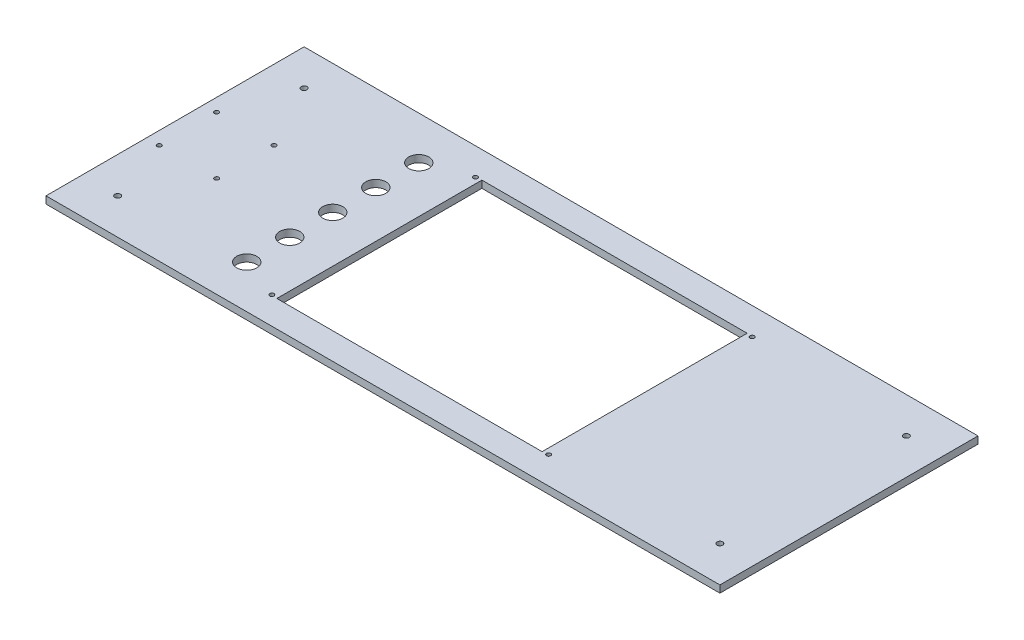
SolidWorks part; units mm, degrees
ref_plane "前视基准面" through (0, 0, 0) normal (0, 0, 1) x (1, 0, 0)
ref_plane "上视基准面" through (0, 0, 0) normal (0, 1, 0) x (1, 0, 0)
ref_plane "右视基准面" through (0, 0, 0) normal (1, 0, 0) x (0, 0, -1)
sketch "草图1" plane through (0, 0, 0) normal (0, 1, 0) x (1, 0, 0)
  line L0 (0, 105) -> (0, -75) construction
  line L1 (-235, 105) -> (235, 105)
  line L2 (-235, 105) -> (-235, -75)
  line L3 (-235, -75) -> (235, -75)
  line L4 (235, 105) -> (235, -75)
  line L5 (-235, 15) -> (235, 15) construction
  line L7 (-92.5, 86.5) -> (92.5, 86.5)
  line L8 (-92.5, 86.5) -> (-92.5, -56.5)
  line L9 (-92.5, -56.5) -> (92.5, -56.5)
  line L10 (92.5, 86.5) -> (92.5, -56.5)
  line L22 (0, 86.5) -> (0, -56.5) construction
  line L23 (-92.5, 15) -> (92.5, 15) construction
  line L24 (-125, 105) -> (-125, -75) construction
  circle A10 centre (-96.5, 86) radius 1.5
  circle A11 centre (96.5, 86) radius 1.5
  circle A12 centre (96.5, -56) radius 1.5
  circle A13 centre (-96.5, -56) radius 1.5
  circle A18 centre (-125, 75) radius 7
  circle A19 centre (-125, 45) radius 7
  circle A20 centre (-125, 15) radius 7
  circle A21 centre (-125, -15) radius 7
  circle A22 centre (-125, -45) radius 7
  circle A23 centre (-226, 35) radius 1.5
  circle A24 centre (-186, 35) radius 1.5
  circle A25 centre (-186, -5) radius 1.5
  circle A26 centre (-226, -5) radius 1.5
  circle A27 centre (-210, -50) radius 2
  circle A28 centre (210, -50) radius 2
  circle A29 centre (-210, 80) radius 2
  circle A30 centre (210, 80) radius 2
  dimension "D17" = 40
  dimension "D18" = 9
  dimension "D20" = 3
  dimension "D22" = 3
  dimension "D30" = 14
  dimension "D10" = 30
  dimension "D11" = 90
  dimension "D21" = 3
  dimension "D29" = 3
  dimension "D32" = 3
  dimension "D33" = 4
  dimension "D36" = 4
  dimension "D39" = 4
  dimension "D42" = 4
  dimension "D1" = 470
  dimension "D2" = 235
  dimension "D3" = 180
  dimension "D4" = 105
  dimension "D5" = 185
  dimension "D6" = 143
  dimension "D7" = 18.5
  dimension "D8" = 92.5
  dimension "D9" = 110
  dimension "D12" = 20
  dimension "D13" = 20
  dimension "D14" = 20
  dimension "D15" = 20
  dimension "D16" = 40
  dimension "D19" = 9
  dimension "D25" = 193
  dimension "D26" = 142
  dimension "D27" = 96.5
  dimension "D28" = 71
  dimension "D34" = 25
  dimension "D35" = 25
  dimension "D37" = 25
  dimension "D38" = 25
  dimension "D40" = 25
  dimension "D41" = 25
  dimension "D23" = 2
  dimension "D24" = 2
  dimension "D31" = 5
extrude "凸台-拉伸1" add sketch "草图1" along normal blind 5
